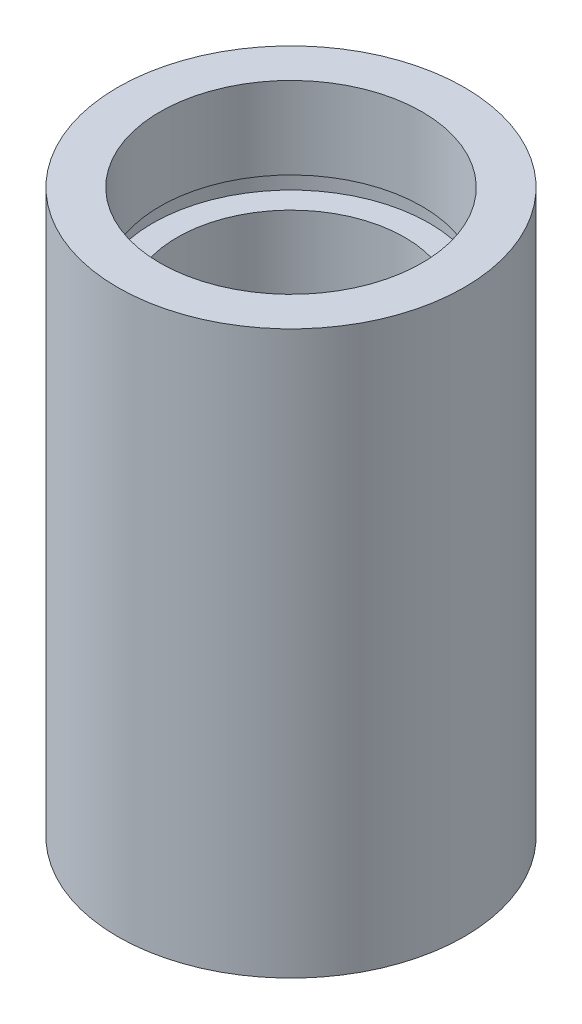
SolidWorks part; units mm, degrees
ref_plane "前视基准面" through (0, 0, 0) normal (0, 0, 1) x (1, 0, 0)
ref_plane "上视基准面" through (0, 0, 0) normal (0, 1, 0) x (1, 0, 0)
ref_plane "右视基准面" through (0, 0, 0) normal (1, 0, 0) x (0, 0, -1)
sketch "草图1" plane through (0, 0, 0) normal (0, 0, 1) x (1, 0, 0)
  line L0 (0, 161.3762) -> (0, 0) construction
  line L1 (141.7365, 0) -> (-131.7984, 0) construction
  line L2 (7, 0) -> (7, 4.5)
  line L3 (7.6, 4.5) -> (7.6, 5.5)
  line L4 (7, 4.5) -> (7.6, 4.5)
  line L5 (6.25, 5.5) -> (6.25, 25.4)
  line L6 (6.25, 5.5) -> (7.6, 5.5)
  line L7 (7.6, 25.4) -> (7.6, 26.4)
  line L8 (6.25, 25.4) -> (7.6, 25.4)
  line L9 (7.2, 26.4) -> (7.2, 30.9)
  line L10 (7.2, 26.4) -> (7.6, 26.4)
  line L11 (9.525, 0) -> (9.525, 30.9)
  line L12 (7, 0) -> (9.525, 0)
  line L13 (7.2, 30.9) -> (9.525, 30.9)
  dimension "D1" = 7
  dimension "D2" = 4.5
  dimension "D3" = 7.6
  dimension "D4" = 6.25
  dimension "D5" = 1
  dimension "D6" = 1
  dimension "D7" = 7.2
  dimension "D8" = 4.5
  dimension "D9" = 9.525
  dimension "D10" = 25.4
revolve "旋转1" add sketch "草图1" angle 360 about L0
cosmetic thread "装饰螺纹线1"
cosmetic thread "装饰螺纹线2"
cosmetic thread "装饰螺纹线3"
